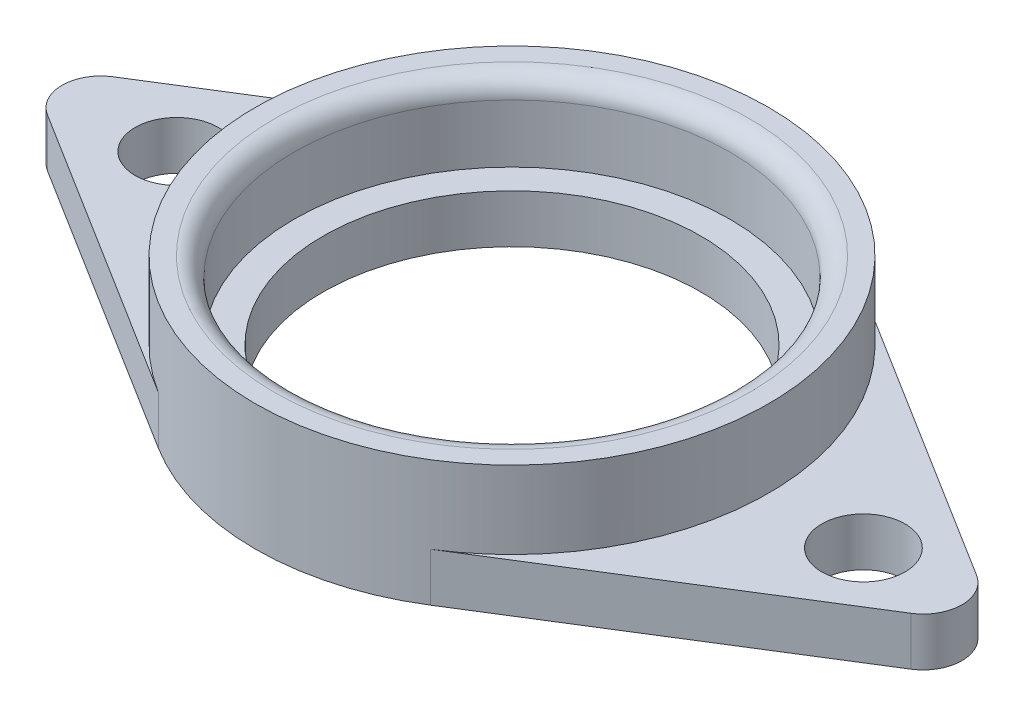
SolidWorks part; units mm, degrees
ref_plane "Plan de face" through (0, 0, 0) normal (0, 0, 1) x (1, 0, 0)
ref_plane "Plan de dessus" through (0, 0, 0) normal (0, 1, 0) x (1, 0, 0)
ref_plane "Plan de droite" through (0, 0, 0) normal (1, 0, 0) x (0, 0, -1)
sketch "Esquisse1" plane through (0, 0, 0) normal (0, 1, 0) x (1, 0, 0)
  line L0 (-25, 0) -> (25, 0) construction
  line L1 (-22.2864, 1.696) -> (-7.0225, 11.236)
  line L2 (7.0225, 11.236) -> (22.2864, 1.696)
  line L3 (22.2864, -1.696) -> (7.0225, -11.236)
  line L4 (-22.2864, -1.696) -> (-7.0225, -11.236)
  circle A0 centre (0, 0) radius 9.75
  arc A1 (22.2864, 1.696) -> (22.2864, -1.696) centre (21.2264, 0) cw
  arc A2 (-22.2864, 1.696) -> (-22.2864, -1.696) centre (-21.2264, 0) ccw
  circle A3 centre (-17.3052, 0) radius 2.15
  circle A4 centre (18.1402, 0) radius 2.15
  circle A5 centre (0, 0) radius 13.25
  point P6 (0, 0)
  point P20 (0, 0)
  point P21 (0, 0)
  point P22 (0, 0)
  point P23 (0, 0)
  point P24 (2.5587, 11.6722)
  point P26 (-12.4478, 5.3163)
  point P27 (-5.0545, 10.6508)
  point P28 (5.0545, 10.6508)
  point P29 (5.0545, -10.6508)
  point P30 (-6.6125, -9.7602)
  point P31 (0, 0)
  point P32 (-17.3052, 0)
  point P33 (18.1402, 0)
  dimension "D1" = 19.5
  dimension "D2" = 2
  dimension "D3" = 4.3
  dimension "D4" = 4.3
  dimension "D6" = 3.5
  dimension "D5" = 50
extrude "Boss.-Extru.1" add sketch "Esquisse1" along normal blind 2.5 contours A2 L0 A3 A5 L1 | L0 A2 L4 A5 A3 | L0 A5 A0 | A5 L0 A4 A1 L2 | L0 A5 L3 A1 A4 | A5 L0 A0
sketch "Esquisse2" plane through (0, 2.5, 0) normal (0, 1, 0) x (1, 0, 0)
  circle A1 centre (0, 0) radius 13.25
  circle A2 centre (0, 0) radius 11.25
  dimension "D1" = 22.5
  dimension "D2" = 2
extrude "Boss.-Extru.2" add sketch "Esquisse2" along normal blind 4
fillet "Congé1" radius 1 1 edges at (0, 6.5, 11.25)
